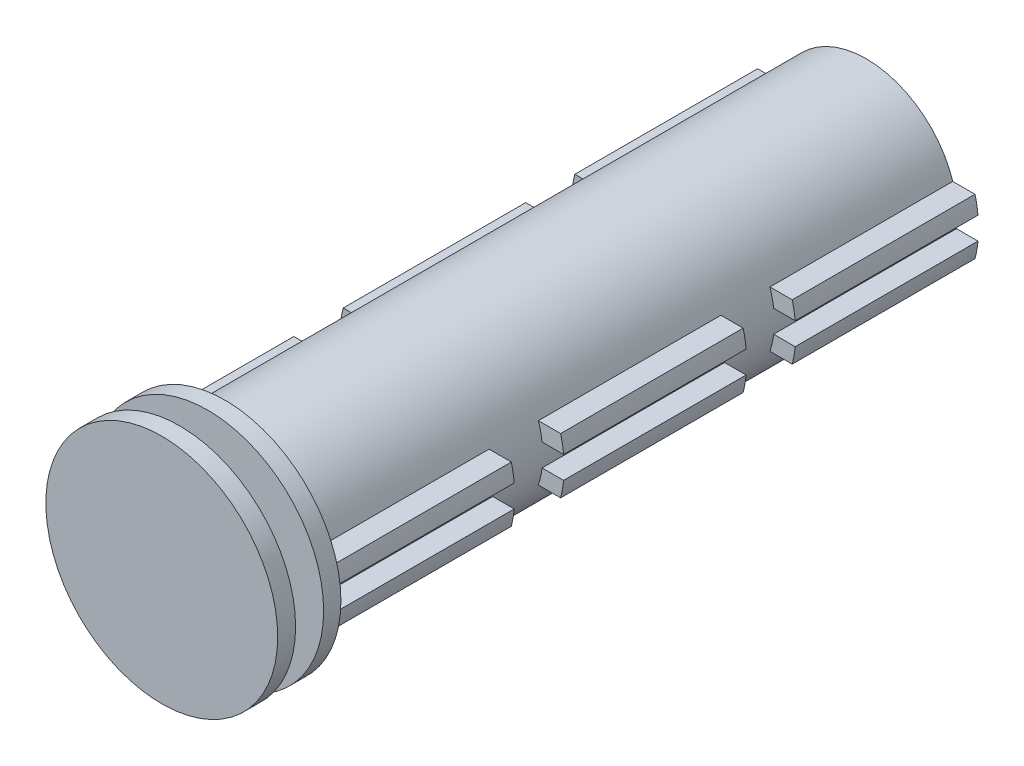
SolidWorks part; units mm, degrees
material "Nylon 101"
ref_plane "Front Plane" through (0, 0, 0) normal (0, 0, 1) x (1, 0, 0)
ref_plane "Top Plane" through (0, 0, 0) normal (0, 1, 0) x (1, 0, 0)
ref_plane "Right Plane" through (0, 0, 0) normal (1, 0, 0) x (0, 0, -1)
sketch "Sketch1" plane through (0, 0, 0) normal (0, 0, 1) x (1, 0, 0)
  circle A0 centre (-78.5195, 2.7413) radius 9.3536
extrude "Boss-Extrude1" add sketch "Sketch1" along normal blind 66.04 contours A0
sketch "Sketch7" plane through (0, 0, 66.04) normal (0, 0, 1) x (1, 0, 0)
  circle A0 centre (-78.5195, 2.7413) radius 11.938
extrude "Boss-Extrude4" add sketch "Sketch7" along normal blind 1.778
ref_plane "Plane2" through (-69.85, 0, 0) normal (1, 0, 0) x (0, 0, -1)
sketch "Sketch12" plane through (-69.85, 0, 0) normal (1, 0, 0) x (0, 0, -1)
  line L0 (-66.04, 5.6115) -> (-66.04, 3.897)
  line L1 (-66.04, 1.5788) -> (-66.04, -0.1289)
  line L2 (0, 1.5856) -> (-18.8248, 1.5856)
  line L3 (-18.8248, 1.5856) -> (-18.8248, -0.1289)
  line L4 (-18.8248, -0.1289) -> (0, -0.1289)
  line L5 (0, -0.1289) -> (0, 1.5856)
  line L6 (0, 5.6115) -> (0, 3.897)
  line L7 (-18.8248, 5.6115) -> (0, 5.6115)
  line L8 (-18.8248, 3.897) -> (-18.8248, 5.6115)
  line L9 (0, 3.897) -> (-18.8248, 3.897)
  line L10 (-23.876, 1.5856) -> (-42.672, 1.5856)
  line L11 (-23.876, -0.1289) -> (-23.876, 1.5856)
  line L12 (-42.672, 1.5856) -> (-42.672, -0.1289)
  line L13 (-42.672, 5.6115) -> (-23.876, 5.6115)
  line L14 (-42.672, 3.897) -> (-42.672, 5.6115)
  line L15 (-23.876, 3.897) -> (-42.672, 3.897)
  line L16 (-42.672, -0.1289) -> (-23.876, -0.1289)
  line L17 (-23.876, 5.6115) -> (-23.876, 3.897)
  line L18 (-47.752, 5.6115) -> (-47.752, 3.897)
  line L19 (-66.04, -0.1289) -> (-47.752, -0.1289)
  line L20 (-66.04, 5.6115) -> (-47.752, 5.6115)
  line L21 (-47.752, -0.1289) -> (-47.752, 1.5788)
  line L22 (-47.752, 3.897) -> (-66.04, 3.897)
  line L23 (-47.752, 1.5788) -> (-66.04, 1.5788)
sketch "Sketch14" plane through (0, 0, 0) normal (0, 0, -1) x (-1, 0, 0)
  circle A0 centre (78.5195, 2.7413) radius 7.7153
extrude "Cut-Extrude1" cut sketch "Sketch14" against normal blind 66.04 contours A0
extrude "Boss-Extrude5" add sketch "Sketch12" along normal blind 2.8448 contours L9 L8 L7 L6 | L0 L22 L18 L20 | L13 L17 L15 L14 | L1 L19 L21 L23 | L10 L12 L16 L11 | L2 L3 L4 L5
sketch "Sketch17" plane through (0, 0, 0) normal (0, 0, -1) x (-1, 0, 0)
  line L0 (66.9625, -0.2507) -> (90.4575, 2.7413)
  line L1 (78.5195, -4.974) -> (78.5195, 6.6348)
  line L2 (69.85, 12.7127) -> (69.85, -12.7127) construction
  line L5 (66.9625, -0.2507) -> (66.9625, 9.1139)
  line L6 (10.2889, 0) -> (-10.2889, 0) construction
  line L9 (75.9795, -6.6123) -> (75.9795, -5.3423)
  line L11 (81.0595, -6.6123) -> (81.0595, -5.3423)
  line L12 (75.9795, -5.3423) -> (81.0595, -5.3423)
  line L13 (75.9795, -6.6123) -> (75.9795, -9.1523)
  line L14 (81.0595, -6.6123) -> (81.0595, -9.1523)
  line L15 (75.9795, -9.1523) -> (81.0595, -9.1523)
  circle A0 centre (78.5195, 2.7413) radius 11.938 construction
  circle A1 centre (78.5195, 2.7413) radius 11.938 construction
  circle A2 centre (78.5195, 2.7413) radius 7.7153 construction
  circle A3 centre (78.5195, 2.7413) radius 7.7153 construction
  arc M5 (69.6172, -0.1289) -> (69.6172, 5.6115) centre (78.5195, 2.7413) ccw
  dimension "D1" = 8.6695
  dimension "D2" = 8.6695
  dimension "D3" = 11.557
  dimension "D4" = 2.7281
ref_plane "Plane3" through (-78.5622, 0, 0) normal (1, 0, 0) x (0, 0, -1)
ref_plane "Plane4" through (-87.1982, 0, 0) normal (1, 0, 0) x (0, 0, -1)
mirror "Mirror2" about plane through (-78.5622, 0, 0) normal (1, 0, 0) of "Boss-Extrude5"
sketch "Sketch19" plane through (0, 0, 0) normal (0, 0, -1) x (-1, 0, 0)
  line L0 (67.0205, 3.897) -> (67.0052, 3.897)
  line L1 (67.0052, 3.897) -> (67.0052, 5.6115)
  line L2 (67.0052, 5.6115) -> (67.3246, 5.6115)
  line L3 (67.0052, 1.5856) -> (67.0205, 1.5856)
  line L5 (67.0052, 1.5856) -> (67.0052, -0.1289)
  line L7 (67.0052, -0.1289) -> (67.3246, -0.1289)
  line L14 (67.0052, 1.5856) -> (69.2377, 1.5856) construction
  line L19 (90.1192, 5.6115) -> (89.7144, 5.6115)
  line L20 (90.1192, 5.6115) -> (90.1192, 3.897)
  line L21 (90.1192, 3.897) -> (90.0186, 3.897)
  line L22 (89.7144, -0.1289) -> (90.1192, -0.1289)
  line L23 (90.1192, -0.1289) -> (90.1192, 1.5856)
  line L24 (90.1192, 1.5856) -> (90.0179, 1.5788)
  arc A0 (67.3246, 5.6115) -> (67.0205, 3.897) centre (78.5195, 2.7413) ccw
  arc A1 (67.0205, 1.5856) -> (67.3246, -0.1289) centre (78.5195, 2.7413) ccw
  arc A5 (67.3246, 5.6115) -> (67.0205, 3.897) centre (78.5195, 2.7413) ccw
  arc A9 (89.7144, 5.6115) -> (90.0186, 3.897) centre (78.5195, 2.7413) cw
  arc A12 (90.0179, 1.5788) -> (89.7144, -0.1289) centre (78.5195, 2.7413) cw
extrude "Cut-Extrude2" cut sketch "Sketch19" against normal blind 66.04
sketch "Sketch21" plane through (0, 0, 67.818) normal (0, 0, 1) x (1, 0, 0)
  line L1 (-78.5622, -18.518) -> (-78.5622, 18.518) construction
  circle A1 centre (-78.5622, 2.7413) radius 7.3995
extrude "Boss-Extrude7" add sketch "Sketch21" along normal blind 2.8448
sketch "Sketch22" plane through (0, 0, 70.6628) normal (0, 0, 1) x (1, 0, 0)
  circle A0 centre (-78.5622, 2.7413) radius 11.938
extrude "Boss-Extrude8" add sketch "Sketch22" along normal blind 1.8415
ref_plane "Plane5" through (0, 2.728, 0) normal (0, 1, 0) x (1, 0, 0)
extrude "Cut-Extrude3" cut sketch "Sketch17" against normal blind 66.04 contours L12 L9 L11 M5
